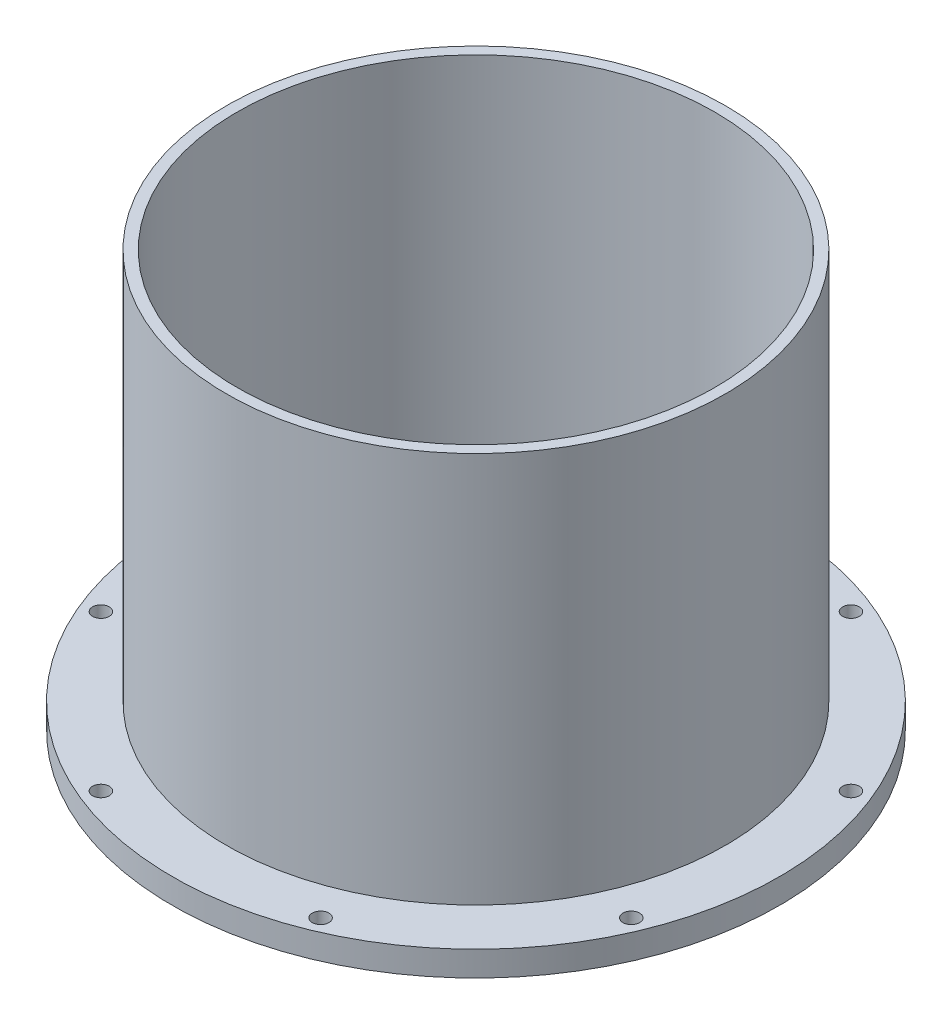
SolidWorks part; units mm, degrees
ref_plane "Front Plane" through (0, 0, 0) normal (0, 0, 1) x (1, 0, 0)
ref_plane "Top Plane" through (0, 0, 0) normal (0, 1, 0) x (1, 0, 0)
ref_plane "Right Plane" through (0, 0, 0) normal (1, 0, 0) x (0, 0, -1)
sketch "Sketch1" plane through (0, 0, 0) normal (0, 0, 1) x (1, 0, 0)
  line L0 (0, 0) -> (0, 250) construction
  line L1 (143.5, 250) -> (143.5, 0)
  line L2 (143.5, 0) -> (182.5, 0)
  line L3 (182.5, 0) -> (182.5, 15)
  line L4 (182.5, 15) -> (150, 15)
  line L5 (150, 15) -> (150, 250)
  line L6 (150, 250) -> (143.5, 250)
  point P6 (0, 265.9532)
  dimension "D1" = 250
  dimension "D2" = 15
  dimension "D3" = 365
  dimension "D4" = 6.5
  dimension "D5" = 287
revolve "Revolve1" add sketch "Sketch1" angle 360 about L0
sketch "Sketch2" plane through (0, 15, 0) normal (0, 1, 0) x (1, 0, 0)
  line L0 (159.3692, 66.0129) -> (0, 0) construction
  circle A0 centre (0, 0) radius 172.5 construction
  circle A1 centre (159.3692, 66.0129) radius 5
  dimension "D1" = 345
  dimension "D2" = 10
  dimension "D3" = 22.5
extrude "Cut-Extrude1" cut sketch "Sketch2" against normal through all both and the other way through all
pattern_circular "CirPattern1" count 8 over 360 about axis through (0, 0, 0) along (0, 1, 0) of "Cut-Extrude1"
